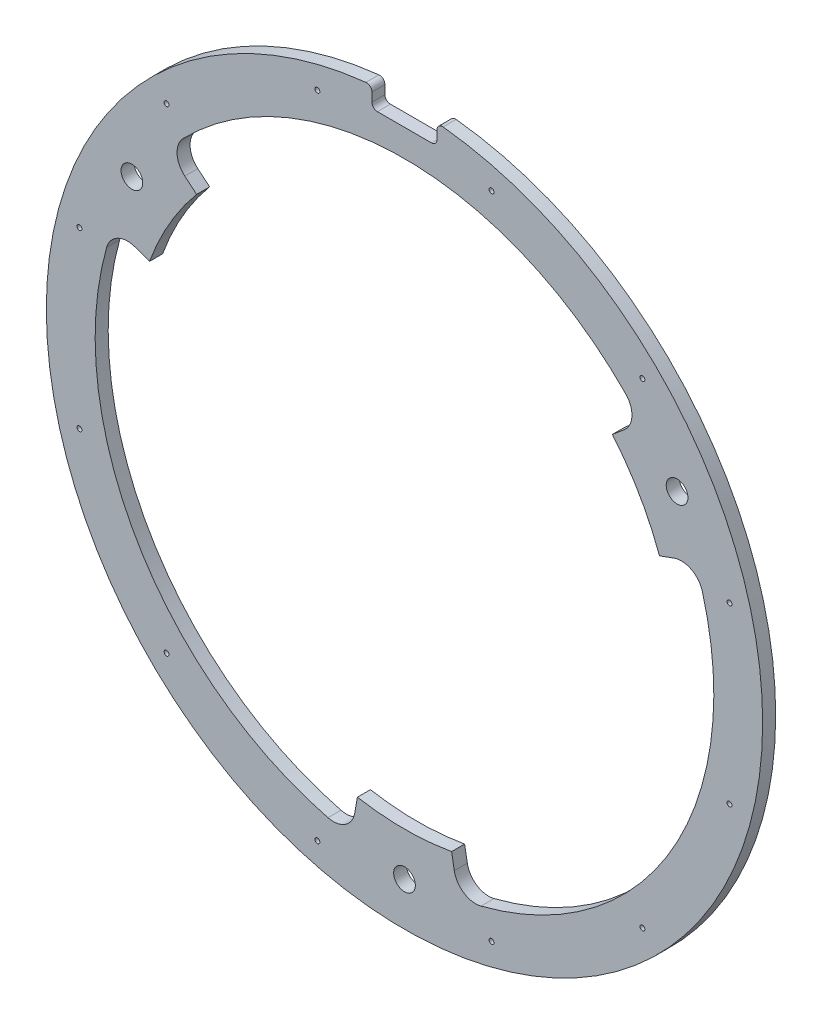
SolidWorks part; units mm, degrees
ref_plane "Front Plane" through (0, 0, 0) normal (0, 0, 1) x (1, 0, 0)
ref_plane "Top Plane" through (0, 0, 0) normal (0, 1, 0) x (1, 0, 0)
ref_plane "Right Plane" through (0, 0, 0) normal (1, 0, 0) x (0, 0, -1)
sketch "Sketch2" plane through (0, 0, 0) normal (0, 0, 1) x (1, 0, 0)
  circle A0 centre (0, 0) radius 330
  circle A2 centre (0, 0) radius 250
  dimension "D1" = 660
  dimension "D2" = 500
extrude "Boss-Extrude1" add sketch "Sketch2" along normal blind 12
sketch "Sketch3" plane through (0, 0, 12) normal (0, 0, 1) x (1, 0, 0)
  line L0 (191.5111, 160.6969) -> (202.4228, 169.8529)
  line L1 (-191.5111, 160.6969) -> (-202.4228, 169.8529)
  line L2 (43.412, -246.2019) -> (45.8855, -260.2297)
  line L4 (234.9232, 85.505) -> (248.3083, 90.3768)
  line L6 (0, 0) -> (0, 240.4153) construction
  line L7 (191.5111, 160.6969) -> (0, 0) construction
  line L8 (-234.9232, 85.505) -> (-248.3083, 90.3768)
  line L9 (-43.412, -246.2019) -> (-45.8855, -260.2297)
  arc A0 (203.874, 199.1492) -> (-203.874, 199.1492) centre (0, 0) ccw
  circle A1 centre (0, 0) radius 250 construction
  arc A2 (191.5111, 160.6969) -> (-191.5111, 160.6969) centre (0, 0) ccw
  arc A3 (-202.4228, 169.8529) -> (-203.874, 199.1492) centre (-189.5671, 185.1738) cw
  arc A4 (202.4228, 169.8529) -> (203.874, 199.1492) centre (189.5671, 185.1738) ccw
  circle A5 centre (0, 0) radius 330 construction
  arc A6 (70.5312, -276.1346) -> (274.4052, 76.9855) centre (0, 0) ccw
  arc A7 (43.412, -246.2019) -> (234.9232, 85.505) centre (0, 0) ccw
  arc A8 (248.3083, 90.3768) -> (274.4052, 76.9855) centre (255.1487, 71.583) cw
  arc A9 (45.8855, -260.2297) -> (70.5312, -276.1346) centre (65.5817, -256.7568) ccw
  arc A10 (-274.4052, 76.9855) -> (-70.5312, -276.1346) centre (0, 0) ccw
  arc A11 (-234.9232, 85.505) -> (-43.412, -246.2019) centre (0, 0) ccw
  arc A12 (-45.8855, -260.2297) -> (-70.5312, -276.1346) centre (-65.5817, -256.7568) cw
  arc A13 (-248.3083, 90.3768) -> (-274.4052, 76.9855) centre (-255.1487, 71.583) ccw
  point P33 (0, 0)
  dimension "D1" = 45
  dimension "D3" = 20
  dimension "D2" = 100
  dimension "D4" = 3
extrude "Cut-Extrude1" cut sketch "Sketch3" against normal blind 12
sketch "Sketch4" plane through (0, 0, 12) normal (0, 0, 1) x (1, 0, 0)
  line L0 (0, 0) -> (0, -290) construction
  circle A0 centre (0, -290) radius 10
  circle A1 centre (-251.1474, 145) radius 10
  circle A2 centre (251.1474, 145) radius 10
  point P11 (0, 0)
  dimension "D1" = 20
  dimension "D2" = 290
  dimension "D3" = 3
extrude "Cut-Extrude2" cut sketch "Sketch4" against normal blind 12
sketch "Sketch5" plane through (0, 0, 12) normal (0, 0, 1) x (1, 0, 0)
  line L0 (0, 0) -> (0, 370) construction
  line L1 (30, 370) -> (30, 310)
  line L2 (30, 370) -> (-30, 370)
  line L4 (30, 310) -> (-30, 310)
  line L5 (-30, 370) -> (-30, 310)
  dimension "D1" = 310
  dimension "D2" = 60
  dimension "D3" = 60
extrude "Cut-Extrude3" cut sketch "Sketch5" against normal blind 12
fillet "Fillet1" radius 5 4 edges at (30, 328.6335, 6) (-30, 328.6335, 6) (30, 310, 6) (-30, 310, 6)
hole_wizard "CSK for M4 Flat Head Machine Screw" positions "Sketch6" profile "Sketch7" countersink size "M4" standard "ANSI Metric" end condition through all
sketch "Sketch6" plane through (0, 0, -24) normal (0, 0, -1) x (1, 0, 0)
  line L0 (80.2339, 299.437) -> (0, 0) construction
  line L2 (0, 0) -> (0, 423.7069) construction
  circle A0 centre (0, 0) radius 310 construction
  point P0 (80.2339, 299.437)
  point P21 (219.2031, 219.2031)
  point P22 (299.437, 80.2339)
  point P23 (299.437, -80.2339)
  point P24 (219.2031, -219.2031)
  point P25 (80.2339, -299.437)
  point P26 (-80.2339, -299.437)
  point P27 (-219.2031, -219.2031)
  point P28 (-299.437, -80.2339)
  point P29 (-299.437, 80.2339)
  point P30 (-219.2031, 219.2031)
  point P31 (-80.2339, 299.437)
  point P32 (0, 0)
sketch "Sketch7" plane through (80.2339, -299.437, -24) normal (1, 0, 0) x (0, 1, 0)
  line L0 (0, 0) -> (0, 36)
  line L1 (0, 36) -> (2.25, 36)
  line L2 (2.25, 36) -> (2.25, 2.45)
  line L3 (2.25, 2.45) -> (4.7, 0)
  line L4 (4.7, 0) -> (0, 0)
  line L5 (-2.25, 2.45) -> (-4.7, 0) construction
  line L6 (0, -6.35) -> (0, 107.95) construction
  dimension "Thru Hole Dia." = 4.5
  dimension "Thru Hole Depth" = 36
  dimension "Near C'Sink Dia." = 9.4
  dimension "Near C'Sink Angle" = 90
